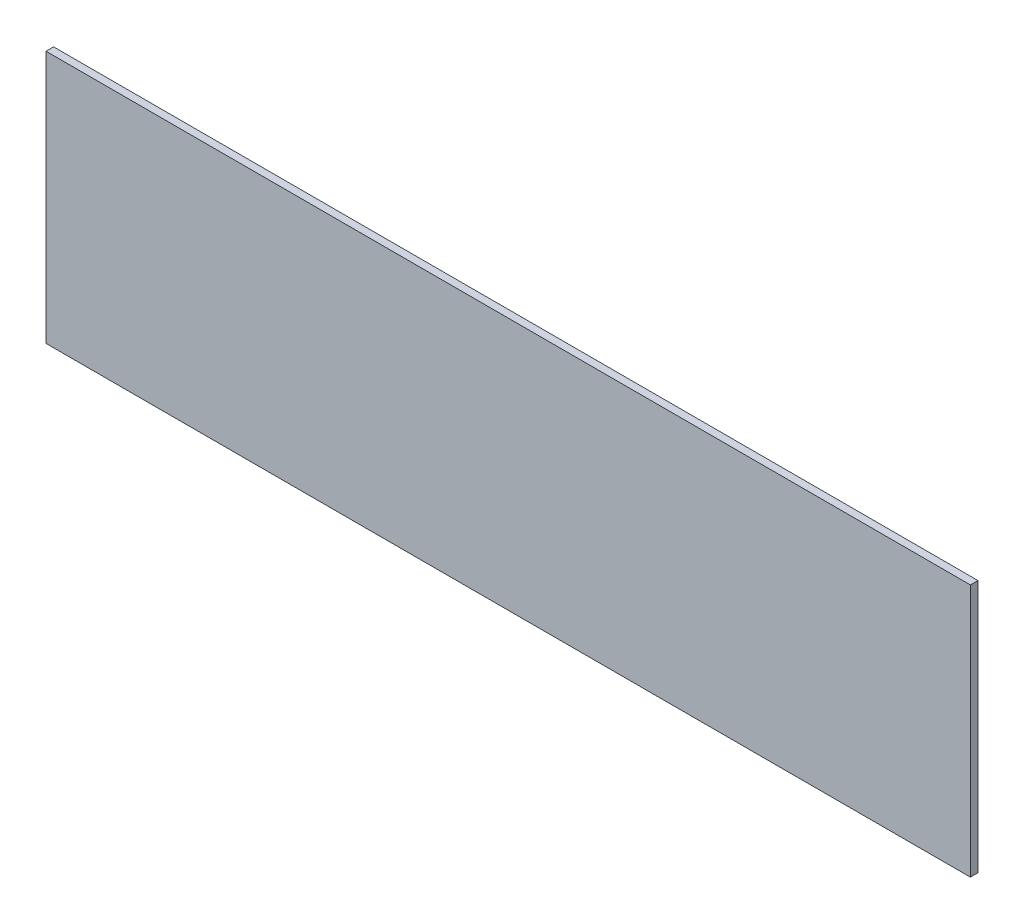
SolidWorks part; units mm, degrees
ref_plane "Front" through (0, 0, 0) normal (0, 0, 1) x (1, 0, 0)
ref_plane "Top" through (0, 0, 0) normal (0, 1, 0) x (1, 0, 0)
ref_plane "Right" through (0, 0, 0) normal (1, 0, 0) x (0, 0, -1)
sketch "Sketch1" plane through (0, 0, 0) normal (0, 0, 1) x (1, 0, 0)
  line L1 (-193.675, 53.0225) -> (193.675, 53.0225)
  line L2 (-193.675, 53.0225) -> (-193.675, -53.0225)
  line L3 (-193.675, -53.0225) -> (193.675, -53.0225)
  line L4 (193.675, 53.0225) -> (193.675, -53.0225)
  point P4 (0, 53.0225)
  point P6 (-193.675, 0)
  dimension "D1" = 387.35
  dimension "D2" = 106.045
extrude "Boss-Extrude1" add sketch "Sketch1" along normal blind 3.175
